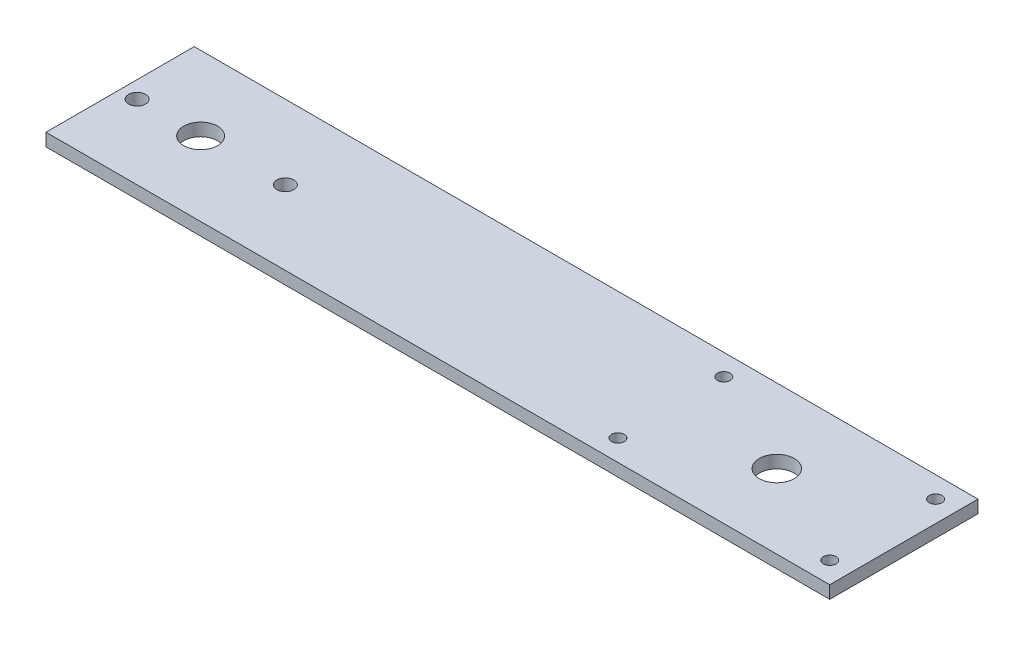
SolidWorks part; units mm, degrees
ref_plane "Front Plane" through (0, 0, 0) normal (0, 0, 1) x (1, 0, 0)
ref_plane "Top Plane" through (0, 0, 0) normal (0, 1, 0) x (1, 0, 0)
ref_plane "Right Plane" through (0, 0, 0) normal (1, 0, 0) x (0, 0, -1)
sketch "Sketch1" plane through (0, 0, 0) normal (0, 1, 0) x (1, 0, 0)
  line L1 (-92.5, 17.5) -> (92.5, 17.5)
  line L2 (-92.5, 17.5) -> (-92.5, -17.5)
  line L3 (-92.5, -17.5) -> (92.5, -17.5)
  line L4 (92.5, 17.5) -> (92.5, -17.5)
  line L5 (-92.5, 17.5) -> (92.5, -17.5) construction
  line L6 (-92.5, -17.5) -> (92.5, 17.5) construction
  circle A4 centre (62.5, 0) radius 4.125
  circle A8 centre (-88.5, 0) radius 2
  circle A9 centre (-53.5, 0) radius 2
  circle A11 centre (-73.5, 0) radius 4
  point P0 (0, 0)
  point P17 (92.5, 0)
  dimension "D3" = 30
  dimension "D4" = 17.5
  dimension "D5" = 15
  dimension "D6" = 8.25
  dimension "D8" = 8
  dimension "D1" = 35
  dimension "D2" = 185
extrude "Boss-Extrude1" add sketch "Sketch1" along normal blind 3
sketch "Sketch2" plane through (0, 3, 0) normal (0, 1, 0) x (1, 0, 0)
  line L0 (-92.5, 17.5) -> (-92.5, -17.5) construction
  line L1 (-92.5, -17.5) -> (92.5, -17.5) construction
  line L2 (-115.5, 6.5) -> (-115.5, -6.7467) construction
  circle A0 centre (-115.5, 6.5) radius 3
  circle A1 centre (-115.5, 6.5) radius 31 construction
  circle A2 centre (-27, 6.5) radius 57.5 construction
  circle A3 centre (-133, -0.5) radius 2
  circle A4 centre (-98, -0.5) radius 2
  dimension "D1" = 6
  dimension "D3" = 24
  dimension "D4" = 7
  dimension "D2" = 23
  dimension "D5" = 17.5
extrude "Cut-Extrude1" [suppressed] cut sketch "Sketch2" against normal through all contours A3 | A4
sketch "Sketch3" plane through (0, 3, 0) normal (0, 1, 0) x (1, 0, 0)
  line L0 (-92.5, -17.5) -> (92.5, -17.5) construction
  line L3 (92.5, 17.5) -> (92.5, -17.5) construction
  line L4 (-55, 0) -> (55, 0) construction
  circle A0 centre (72.5, -9.5) radius 1.5
  circle A3 centre (72.5, 9.5) radius 1.5
  dimension "D1" = 3
  dimension "D2" = 8
  dimension "D3" = 20
extrude "Cut-Extrude2" [suppressed] cut sketch "Sketch3" against normal through all
sketch "Sketch4" plane through (0, 3, 0) normal (0, 1, 0) x (1, 0, 0)
  line L0 (-92.5, 17.5) -> (92.5, 17.5) construction
  line L1 (62.5, 0) -> (41.5, 0) construction
  line L2 (92.5, 17.5) -> (92.5, -17.5) construction
  line L3 (-55, 0) -> (55, 0) construction
  circle A1 centre (52.5, 9.5) radius 1.5
  circle A2 centre (52.5, -9.5) radius 1.5
  dimension "D2" = 8
  dimension "D4" = 3
  dimension "D1" = 21
  dimension "D3" = 40
extrude "Cut-Extrude3" [suppressed] cut sketch "Sketch4" against normal through all
sketch "Sketch5" plane through (0, 3, 0) normal (0, 1, 0) x (1, 0, 0)
  line L0 (-64.8339, 7.0101) -> (-80.04, -19.3277) construction
  line L1 (-92.5, 17.5) -> (-92.5, -17.5) construction
  circle A0 centre (-73.5, 0) radius 4 construction
  circle A1 centre (-62.8075, 10.52) radius 1.5
  circle A2 centre (-77.2643, -14.52) radius 1.5
  dimension "D1" = 3
  dimension "D2" = 3
  dimension "D4" = 15
  dimension "D5" = 15
  dimension "D3" = 30
extrude "Cut-Extrude5" [suppressed] cut sketch "Sketch5" against normal through all
sketch "Sketch6" plane through (0, 3, 0) normal (0, 1, 0) x (1, 0, 0)
  line L0 (-92.5, 17.5) -> (92.5, 17.5) construction
  line L1 (92.5, 17.5) -> (92.5, -17.5) construction
  line L2 (-55, 0) -> (55, 0) construction
  line L3 (62.5, 0) -> (62.5, 14.7754) construction
  circle A0 centre (87.5, 12.5) radius 1.5
  circle A1 centre (87.5, -12.5) radius 1.5
  circle A2 centre (37.5, -12.5) radius 1.5
  circle A3 centre (37.5, 12.5) radius 1.5
  dimension "D3" = 3
  dimension "D1" = 5
  dimension "D2" = 5
extrude "Cut-Extrude6" cut sketch "Sketch6" against normal through all
